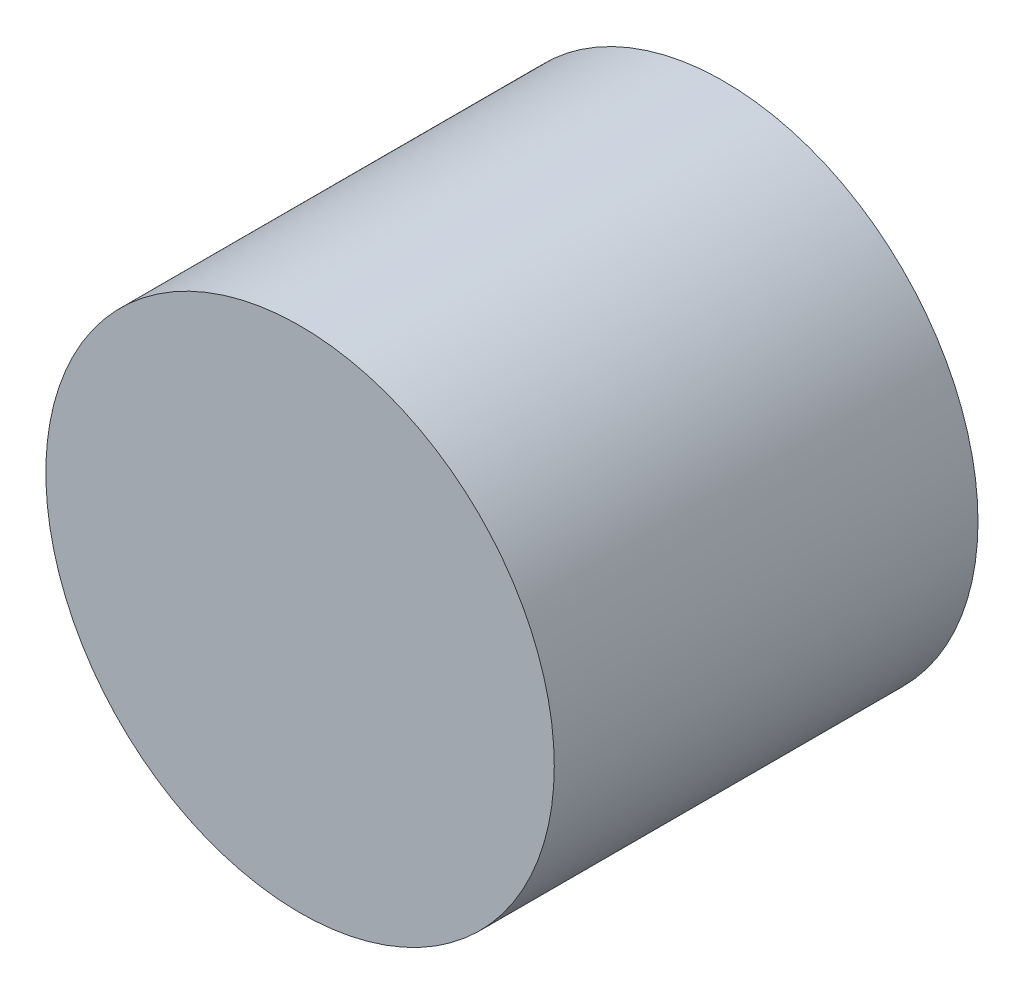
SolidWorks part; units mm, degrees
ref_plane "Front Plane" through (0, 0, 0) normal (1, 0, 0) x (0, 1, 0)
ref_plane "Top Plane" through (0, 0, 0) normal (0, 0, 1) x (0, 1, 0)
ref_plane "Right Plane" through (0, 0, 0) normal (0, 1, 0) x (-1, 0, 0)
sketch "Sketch1" plane through (0, 0, 0) normal (0, 0, 1) x (0, 1, 0)
  circle A0 centre (0, 0) radius 6
  dimension "D1" = 12
extrude "Boss-Extrude1" add sketch "Sketch1" along normal blind 10
